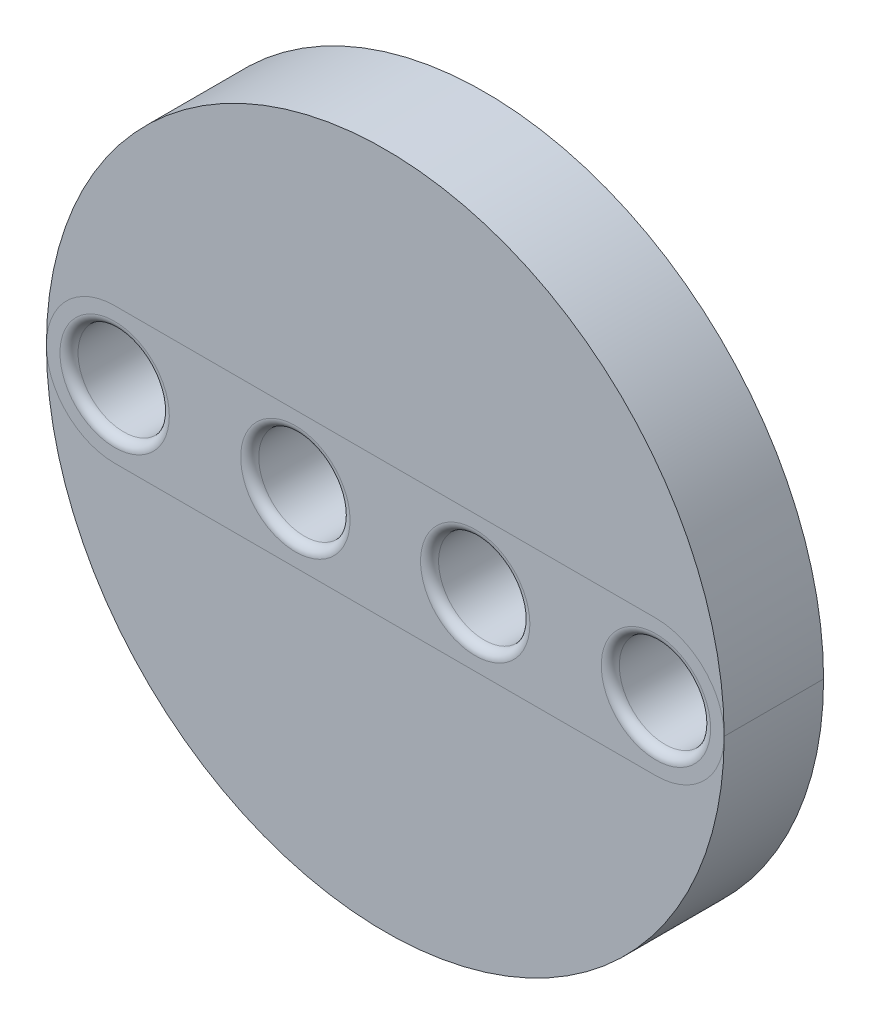
SolidWorks part; units mm, degrees
ref_plane "Front Plane" through (0, 0, 0) normal (0, 0, 1) x (1, 0, 0)
ref_plane "Top Plane" through (0, 0, 0) normal (0, 1, 0) x (1, 0, 0)
ref_plane "Right Plane" through (0, 0, 0) normal (1, 0, 0) x (0, 0, -1)
sketch "Sketch1" plane through (0, 0, 0) normal (0, 0, 1) x (1, 0, 0)
  line L0 (0, 0) -> (59.9, 0) construction
  line L1 (0, 7.55) -> (59.9, 7.55)
  line L2 (0, -7.55) -> (59.9, -7.55)
  arc A0 (0, 7.55) -> (0, -7.55) centre (0, 0) ccw
  arc A1 (59.9, -7.55) -> (59.9, 7.55) centre (59.9, 0) ccw
  circle A2 centre (0, 0) radius 5.05 construction
  circle A3 centre (59.9, 0) radius 5.05 construction
  circle A4 centre (29.95, 0) radius 2.55
  circle A5 centre (0, 0) radius 2.55
  circle A6 centre (59.9, 0) radius 2.55
  circle A7 centre (20, 0) radius 2.55
  circle A8 centre (39.9, 0) radius 2.55
  circle A9 centre (20, 0) radius 5.05 construction
  circle A10 centre (39.9, 0) radius 5.05 construction
  point P3 (29.95, 0)
  dimension "D1" = 10.1
  dimension "D2" = 10.1
  dimension "D3" = 2.5
  dimension "D5" = 5.1
  dimension "D6" = 5.1
  dimension "D7" = 5.1
  dimension "D10" = 10.1
  dimension "D11" = 10.1
  dimension "D12" = 5.1
  dimension "D13" = 5.1
  dimension "D4" = 59.9
  dimension "D8" = 9.95
  dimension "D9" = 9.95
extrude "Boss-Extrude1" add sketch "Sketch1" along normal blind 11
sketch "Sketch2" plane through (0, 0, 11) normal (0, 0, 1) x (1, 0, 0)
  circle A0 centre (0, 0) radius 5.05
  circle A1 centre (59.9, 0) radius 5.05
  circle A2 centre (20, 0) radius 5.05
  circle A3 centre (39.9, 0) radius 5.05
  dimension "D1" = 10.1
  dimension "D2" = 10.1
  dimension "D3" = 10.1
  dimension "D4" = 10.1
extrude "Cut-Extrude1" cut sketch "Sketch2" against normal blind 10
sketch "Sketch3" plane through (0, 0, 11) normal (0, 0, 1) x (1, 0, 0)
  circle A0 centre (29.95, 0) radius 2.55
  circle A1 centre (29.95, 0) radius 2.55 construction
extrude "Boss-Extrude2" add sketch "Sketch3" against normal blind 1
sketch "Sketch4" plane through (0, 0, 11) normal (0, 0, 1) x (1, 0, 0)
  line L0 (29.95, 7.55) -> (29.95, -7.55) construction
  line L1 (59.9, 7.55) -> (0, 7.55) construction
  line L2 (0, -7.55) -> (59.9, -7.55) construction
  circle A0 centre (29.95, 0) radius 37.5
  arc A3 (59.9, -7.55) -> (59.9, 7.55) centre (59.9, 0) ccw construction
  arc M3 (0, 7.55) -> (0, -7.55) centre (0, 0) ccw
  line M4 (0, -7.55) -> (59.9, -7.55)
  arc M5 (59.9, -7.55) -> (59.9, 7.55) centre (59.9, 0) ccw
  line M6 (59.9, 7.55) -> (0, 7.55)
extrude "Boss-Extrude3" add sketch "Sketch4" against normal up to surface (11 mm away) separate body contours A0 M3 M5 M4 | A0 M5 M3 M6 up to face at (29.95, 0, 0)
fillet "Fillet1" radius 1 5 edges at (32.5, 0, 0) (64.95, 0, 11) (5.05, 0, 11) (44.95, 0, 11) (25.05, 0, 11)
